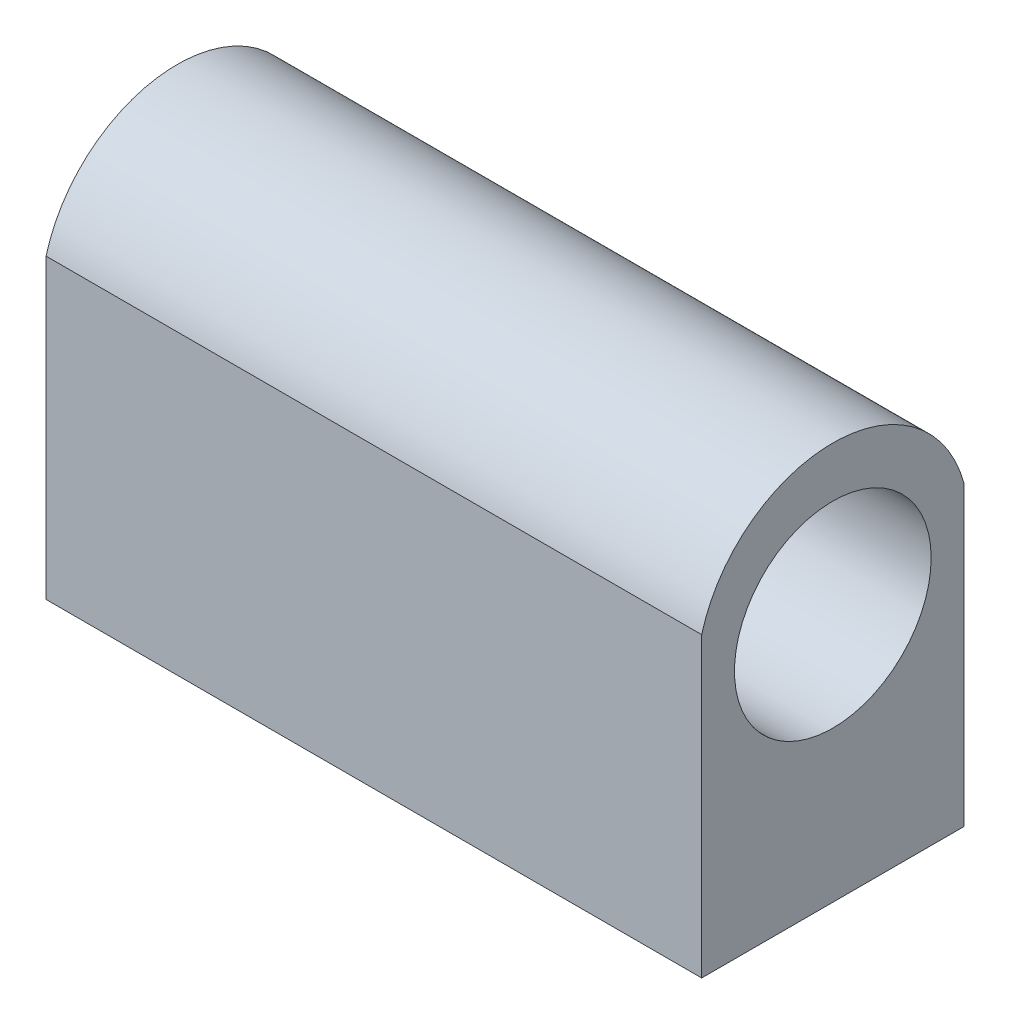
SolidWorks part; units mm, degrees
ref_plane "Front Plane" through (0, 0, 0) normal (0, 0, 1) x (1, 0, 0)
ref_plane "Top Plane" through (0, 0, 0) normal (0, 1, 0) x (1, 0, 0)
ref_plane "Right Plane" through (0, 0, 0) normal (1, 0, 0) x (0, 0, -1)
sketch "Sketch1" plane through (0, 0, 0) normal (0, 1, 0) x (1, 0, 0)
  line L0 (0, -55) -> (0, 55) construction
  line L1 (-25, 10) -> (25, 10)
  line L2 (-25, 10) -> (-25, -10)
  line L3 (-25, -10) -> (25, -10)
  line L4 (25, 10) -> (25, -10)
  line L5 (-55, 0) -> (55, 0) construction
  dimension "D1" = 50
  dimension "D2" = 25
  dimension "D3" = 20
  dimension "D4" = 10
extrude "Boss-Extrude1" add sketch "Sketch1" along normal blind 44
sketch "Sketch3" plane through (0, 0, 0) normal (1, 0, 0) x (0, 0, -1)
  line L0 (0, 55) -> (0, -55) construction
  line L1 (-10, 44) -> (10, 44) construction
  circle A0 centre (0, 19) radius 7.5
  dimension "D1" = 15
  dimension "D2" = 25
extrude "Cut-Extrude3" cut sketch "Sketch3" against normal through all both and the other way through all
sketch "Sketch4" plane through (0, 0, 0) normal (1, 0, 0) x (0, 0, -1)
  line L0 (-10, 44) -> (-10, 0) construction
  line L1 (10, 44) -> (10, 0) construction
  line L2 (-10, 22.6773) -> (-10, 44)
  line L3 (-10, 44) -> (10, 44)
  line L4 (10, 44) -> (10, 22.6773)
  arc A0 (-10, 22.6773) -> (10, 22.6773) centre (0, 19.9813) cw
extrude "Cut-Extrude4" cut sketch "Sketch4" against normal through all both and the other way through all contours L2 A0 L3 | L3 A0 L4
